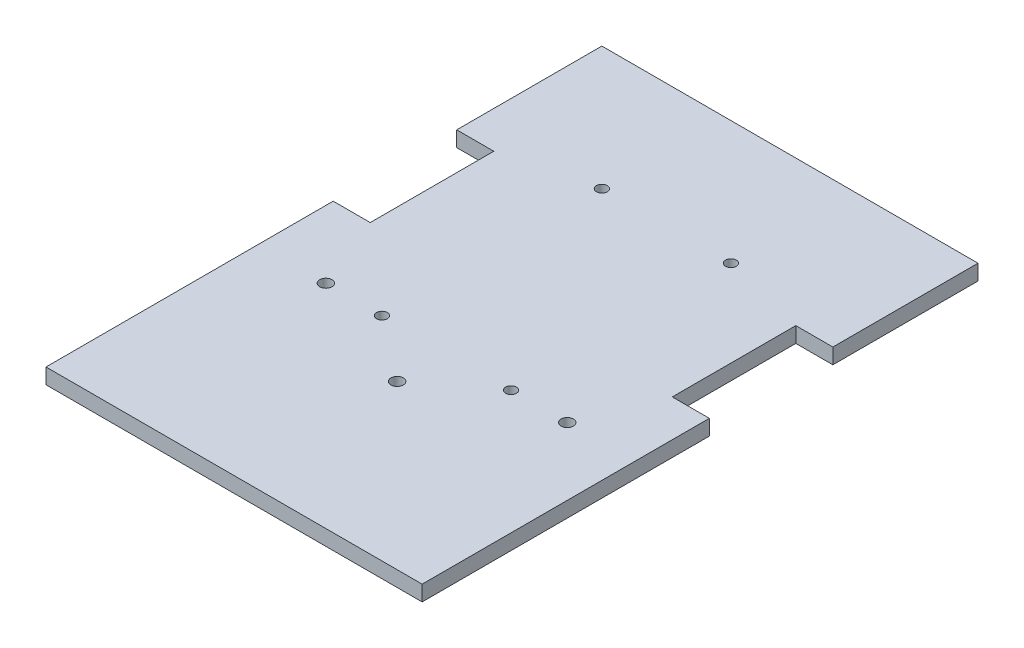
SolidWorks part; units mm, degrees
ref_plane "Front Plane" through (0, 0, 0) normal (0, 0, 1) x (1, 0, 0)
ref_plane "Top Plane" through (0, 0, 0) normal (0, 1, 0) x (1, 0, 0)
ref_plane "Right Plane" through (0, 0, 0) normal (1, 0, 0) x (0, 0, -1)
sketch "Sketch1" plane through (0, 0, 0) normal (0, 1, 0) x (1, 0, 0)
  circle A0 centre (0, 90.4441) radius 2.2225
  circle A1 centre (53.086, 90.4441) radius 2.2225
  circle A2 centre (0, 0) radius 2.2225
  circle A3 centre (53.086, 0) radius 2.2225
  dimension "D1" = 4.445
  dimension "D2" = 4.445
  dimension "D3" = 4.445
  dimension "D4" = 4.445
  dimension "D5" = 53.086
  dimension "D6" = 90.4441
  dimension "D7" = 104.8725
  dimension "D8" = 0
  dimension "D10" = 104.8725
  dimension "D11" = 53.086
  dimension "D9" = 53.086
sketch "Sketch2" plane through (0, 0, 0) normal (0, 1, 0) x (1, 0, 0)
  line L1 (-50.8, 141.2441) -> (103.886, 141.2441)
  line L2 (-50.8, 141.2441) -> (-50.8, -87.3559)
  line L3 (-50.8, -87.3559) -> (103.886, -87.3559)
  line L4 (103.886, 141.2441) -> (103.886, -87.3559)
  circle A0 centre (0, 90.4441) radius 2.2225 construction
  circle A1 centre (53.086, 90.4441) radius 2.2225 construction
  dimension "D3" = 50.8
  dimension "D1" = 50.8
  dimension "D2" = 50.8
  dimension "D4" = 228.6
extrude "Boss-Extrude1" add sketch "Sketch2" along normal blind 6.35
extrude "Cut-Extrude1" cut sketch "Sketch1" along normal blind 6.35
sketch "Sketch3" plane through (0, 6.35, 0) normal (0, 1, 0) x (1, 0, 0)
  line L0 (103.886, -87.3559) -> (103.886, 141.2441) construction
  line L1 (103.886, 81.5541) -> (88.646, 81.5541)
  line L2 (103.886, 81.5541) -> (103.886, 30.7541)
  line L3 (103.886, 30.7541) -> (88.646, 30.7541)
  line L4 (88.646, 81.5541) -> (88.646, 30.7541)
  line L5 (-50.8, 141.2441) -> (-50.8, -87.3559) construction
  line L6 (-50.8, 81.5541) -> (-35.56, 81.5541)
  line L7 (-50.8, 81.5541) -> (-50.8, 30.7541)
  line L8 (-50.8, 30.7541) -> (-35.56, 30.7541)
  line L9 (-35.56, 81.5541) -> (-35.56, 30.7541)
  circle A0 centre (0, 90.4441) radius 2.2225 construction
  point P12 (96.266, 81.5541)
  dimension "D1" = 15.24
  dimension "D2" = 15.24
  dimension "D3" = 0
  dimension "D4" = 50.8
  dimension "D5" = 50.8
  dimension "D6" = 8.89
extrude "Cut-Extrude2" cut sketch "Sketch3" against normal blind 6.35
sketch "Sketch8" plane through (0, 6.35, 0) normal (0, 1, 0) x (1, 0, 0)
  circle A0 centre (26.5501, -20.2997) radius 2.54
  circle A1 centre (-23.0771, 0.0203) radius 2.54
  circle A2 centre (76.1773, 0.0203) radius 2.54
  dimension "D1" = 5.08
  dimension "D2" = 5.08
  dimension "D3" = 5.08
  dimension "D4" = 49.6272
  dimension "D5" = 20.32
  dimension "D6" = 49.6272
  dimension "D7" = 20.32
  dimension "D9" = 26.5501
  dimension "D8" = 20.2997
extrude "Cut-Extrude3" cut sketch "Sketch8" against normal blind 17.78
